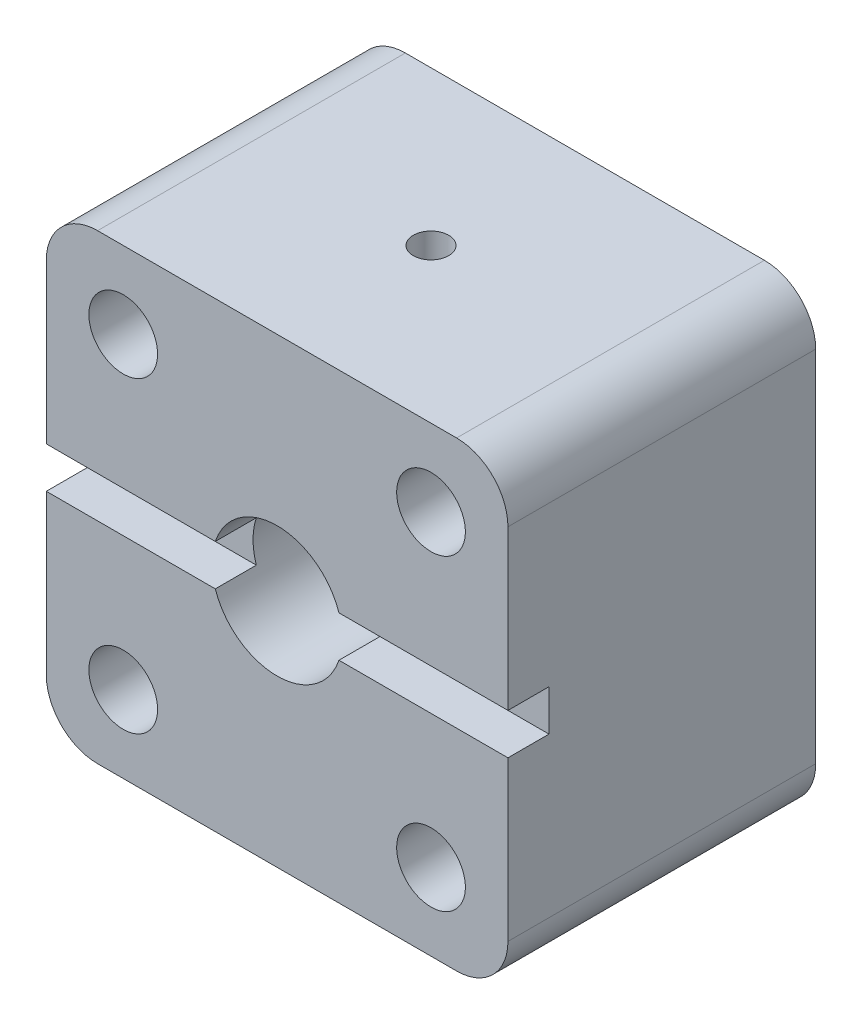
SolidWorks part; units mm, degrees
ref_plane "Front Plane" through (0, 0, 0) normal (0, 0, 1) x (1, 0, 0)
ref_plane "Top Plane" through (0, 0, 0) normal (0, 1, 0) x (1, 0, 0)
ref_plane "Right Plane" through (0, 0, 0) normal (1, 0, 0) x (0, 0, -1)
sketch "Sketch1" plane through (0, 0, 0) normal (0, 0, 1) x (1, 0, 0)
  line L1 (0, 0) -> (45, 0)
  line L2 (0, 0) -> (0, 45)
  line L3 (0, 45) -> (45, 45)
  line L4 (45, 0) -> (45, 45)
  dimension "D1" = 45
  dimension "D2" = 45
extrude "Boss-Extrude1" add sketch "Sketch1" along normal blind 30
sketch "Sketch2" plane through (0, 0, 0) normal (0, 0, -1) x (-1, 0, 0)
  line L0 (-22.5, 45) -> (-22.5, 0) construction
  line L1 (-45, 45) -> (0, 45) construction
  line L2 (0, 0) -> (-45, 0) construction
  line L3 (0, 22.5) -> (-45, 22.5) construction
  line L4 (0, 45) -> (0, 0) construction
  line L5 (-45, 0) -> (-45, 45) construction
  circle A0 centre (-37.5, 37.5) radius 3.35
  circle A1 centre (-7.5, 37.5) radius 3.35
  circle A2 centre (-37.5, 7.5) radius 3.35
  circle A3 centre (-7.5, 7.5) radius 3.35
  dimension "D1" = 15
  dimension "D9" = 6.7
  dimension "D10" = 6.7
  dimension "D11" = 6.7
  dimension "D12" = 6.7
  dimension "D2" = 15
  dimension "D3" = 15
  dimension "D4" = 15
  dimension "D5" = 15
  dimension "D6" = 15
  dimension "D7" = 15
  dimension "D8" = 15
extrude "Cut-Extrude1" cut sketch "Sketch2" against normal through all
sketch "Sketch3" plane through (45, 0, 0) normal (1, 0, 0) x (0, 0, -1)
  line L0 (-15, 45) -> (-15, 0) construction
  line L1 (-30, 45) -> (0, 45) construction
  line L2 (-30, 0) -> (0, 0) construction
  line L3 (-30, 22.5) -> (0, 22.5) construction
  line L4 (-30, 0) -> (-30, 45) construction
  line L5 (0, 0) -> (0, 45) construction
  line L7 (-30, 24.5) -> (-26, 24.5)
  line L8 (-30, 24.5) -> (-30, 20.5)
  line L9 (-30, 20.5) -> (-26, 20.5)
  line L10 (-26, 24.5) -> (-26, 20.5)
  dimension "D1" = 4
  dimension "D2" = 4
  dimension "D3" = 2
extrude "PiezoWireFeedthrough" cut sketch "Sketch3" against normal through all
hole_wizard "AlignmentHole" positions "Sketch5" profile "Sketch4" tap size "#8-32" standard "ANSI Inch"
sketch "Sketch5" plane through (0, 45, 0) normal (0, 1, 0) x (1, 0, 0)
  line L10 (0, -30) -> (0, 0) construction
  line L12 (0, -15) -> (45, -15) construction
  line L13 (45, -30) -> (45, 0) construction
  line L15 (22.5, -30) -> (22.5, 0) construction
  line L16 (45, -30) -> (0, -30) construction
  line L17 (45, 0) -> (0, 0) construction
  point P0 (22.5, -15)
  dimension "D1" = 0
  dimension "D2" = 0
sketch "Sketch4" plane through (22.5, 45, 15) normal (1, 0, 0) x (0, 0, 1)
  line L0 (0, 0) -> (0, 11.0378)
  line L1 (0, 11.0378) -> (1.7272, 10)
  line L2 (1.7272, 10) -> (1.7272, 0)
  line L5 (1.7272, 0) -> (0, 0)
  line L10 (0, 11.0378) -> (-1.7272, 10) construction
  line L11 (0, -6.35) -> (0, 107.95) construction
  dimension "Tap Drill Dia." = 3.4544
  dimension "Tap Drill Depth" = 10
  dimension "Drill Angle" = 118
cosmetic thread "Hole Thread1" parameters "D1"=8.33, "D2"=4.1656
hole_wizard "0.535-40 Tapped Hole1" positions "Sketch6" profile "Sketch7" tap size "0.535-40" standard "Thorlabs" end condition through all
sketch "Sketch6" plane through (0, 0, 0) normal (0, 0, -1) x (-1, 0, 0)
  line L0 (-22.5, 45) -> (-22.5, 0) construction
  line L1 (-45, 45) -> (0, 45) construction
  line L2 (0, 0) -> (-45, 0) construction
  line L4 (-45, 22.5) -> (0, 22.5) construction
  line L5 (-45, 0) -> (-45, 45) construction
  line L6 (0, 45) -> (0, 0) construction
  point P0 (-22.5, 22.5)
  dimension "D1" = 0
  dimension "D2" = 0
cosmetic thread "Hole Thread2" parameters "D2"=13.589
sketch "Sketch7" plane through (22.5, 22.5, 0) normal (1, 0, 0) x (0, 1, 0)
  line L0 (0, 0) -> (0, 30)
  line L1 (0, 30) -> (6.35, 30)
  line L2 (6.35, 30) -> (6.35, 0)
  line L5 (6.35, 0) -> (0, 0)
  line L11 (0, -6.35) -> (0, 107.95) construction
  dimension "Thru Tap Drill Dia." = 12.7
  dimension "Thru Tap Drill Depth" = 30
fillet "Fillet1" radius 5 4 edges at (0, 45, 15) (0, 0, 15) (45, 0, 15) (45, 45, 15)
